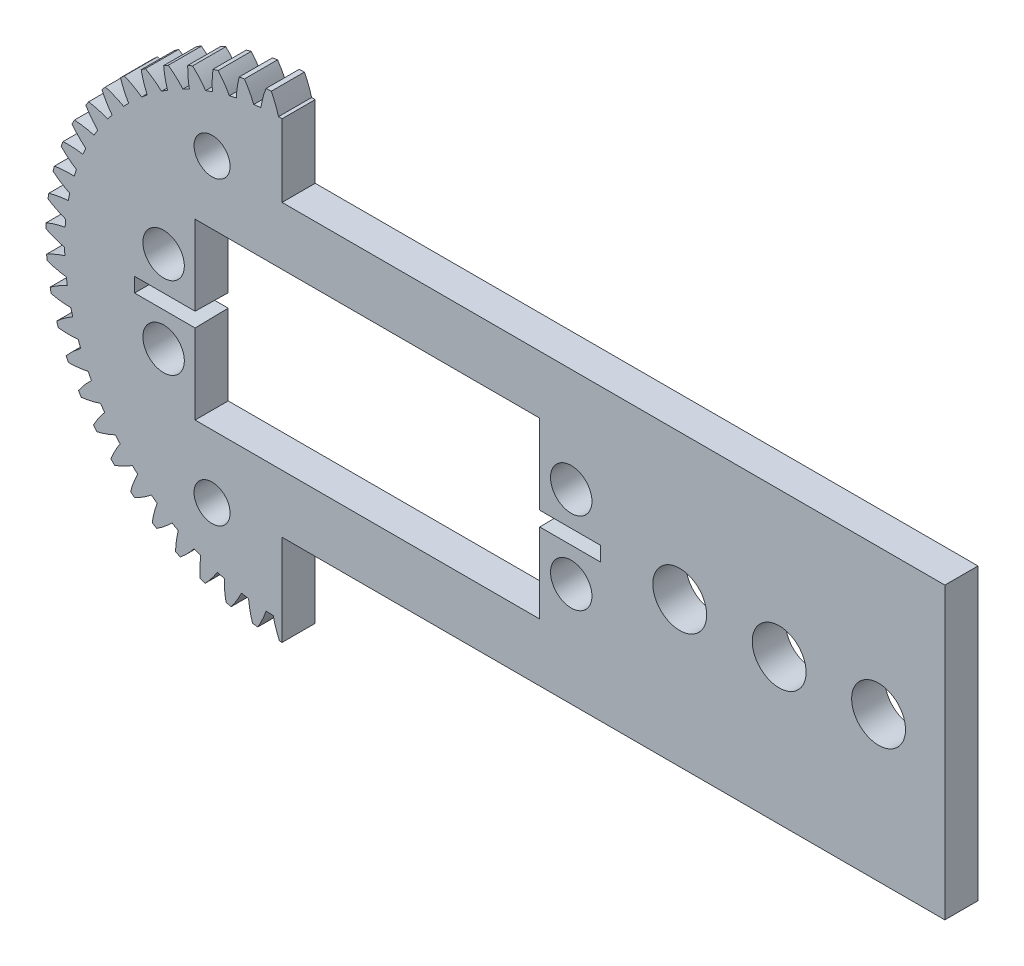
SolidWorks part; units mm, degrees
ref_plane "Front Plane" through (0, 0, 0) normal (0, 0, 1) x (1, 0, 0)
ref_plane "Top Plane" through (0, 0, 0) normal (0, 1, 0) x (1, 0, 0)
ref_plane "Right Plane" through (0, 0, 0) normal (1, 0, 0) x (0, 0, -1)
sketch "Model" plane through (0, 0, 0) normal (0, 0, 1) x (1, 0, 0)
  circle A0 centre (0, 0) radius 2.5
  arc A1 (-28.4774, 1.1339) -> (-28.4957, 0.4937) centre (0, 0) ccw
  arc A2 (-26.1862, 1.814) -> (-28.4774, 1.1339) centre (-24.2203, -9.0089) ccw
  arc A3 (-26.112, 2.6779) -> (-26.1862, 1.814) centre (0, 0) ccw
  arc A4 (-28.2537, 3.7387) -> (-26.112, 2.6779) centre (-22.3294, 13.0071) ccw
  arc A5 (-28.1626, 4.3727) -> (-28.2537, 3.7387) centre (0, 0) ccw
  arc A6 (-25.8088, 4.7871) -> (-28.1626, 4.3727) centre (-25.0894, -6.1893) ccw
  arc A7 (-25.6366, 5.637) -> (-25.8088, 4.7871) centre (0, 0) ccw
  arc A8 (-27.6434, 6.9351) -> (-25.6366, 5.637) centre (-20.7011, 15.4677) ccw
  arc A9 (-27.4805, 7.5545) -> (-27.6434, 6.9351) centre (0, 0) ccw
  arc A10 (-25.0949, 7.6979) -> (-27.4805, 7.5545) centre (-25.6314, -3.289) ccw
  arc A11 (-24.8269, 8.5226) -> (-25.0949, 7.6979) centre (0, 0) ccw
  arc A12 (-26.6726, 10.041) -> (-24.8269, 8.5226) centre (-18.803, 17.7266) ccw
  arc A13 (-26.4403, 10.6378) -> (-26.6726, 10.041) centre (0, 0) ccw
  arc A14 (-24.0538, 10.5083) -> (-26.4403, 10.6378) centre (-25.8392, -0.3458) ccw
  arc A15 (-23.6936, 11.2971) -> (-24.0538, 10.5083) centre (0, 0) ccw
  arc A16 (-25.3542, 13.016) -> (-23.6936, 11.2971) centre (-16.6598, 19.7544) ccw
  arc A17 (-25.0553, 13.5824) -> (-25.3542, 13.016) centre (0, 0) ccw
  arc A18 (-22.6991, 13.1818) -> (-25.0553, 13.5824) centre (-25.7102, 2.6019) ccw
  arc A19 (-22.2513, 13.9244) -> (-22.6991, 13.1818) centre (0, 0) ccw
  arc A20 (-23.7052, 15.8213) -> (-22.2513, 13.9244) centre (-14.2993, 21.5247) ccw
  arc A21 (-23.3437, 16.35) -> (-23.7052, 15.8213) centre (0, 0) ccw
  arc A22 (-21.0486, 15.6834) -> (-23.3437, 16.35) centre (-25.246, 5.5157) ccw
  arc A23 (-20.519, 16.3701) -> (-21.0486, 15.6834) centre (0, 0) ccw
  arc A24 (-21.7472, 18.4203) -> (-20.519, 16.3701) centre (-11.7525, 23.0144) ccw
  arc A25 (-21.3278, 18.9044) -> (-21.7472, 18.4203) centre (0, 0) ccw
  arc A26 (-19.1236, 17.9805) -> (-21.3278, 18.9044) centre (-24.4527, 8.3576) ccw
  arc A27 (-18.5192, 18.6024) -> (-19.1236, 17.9805) centre (0, 0) ccw
  arc A28 (-19.5057, 20.7793) -> (-18.5192, 18.6024) centre (-9.0524, 24.2041) ccw
  arc A29 (-19.0338, 21.2123) -> (-19.5057, 20.7793) centre (0, 0) ccw
  arc A30 (-16.9493, 20.0432) -> (-19.0338, 21.2123) centre (-23.3407, 11.0905) ccw
  arc A31 (-16.278, 20.5921) -> (-16.9493, 20.0432) centre (0, 0) ccw
  arc A32 (-17.0099, 22.8673) -> (-16.278, 20.5921) centre (-6.2344, 25.0782) ccw
  arc A33 (-16.4918, 23.2438) -> (-17.0099, 22.8673) centre (0, 0) ccw
  arc A34 (-14.5541, 21.8446) -> (-16.4918, 23.2438) centre (-21.9243, 13.6788) ccw
  arc A35 (-13.8246, 22.3135) -> (-14.5541, 21.8446) centre (0, 0) ccw
  arc A36 (-14.2923, 24.6572) -> (-13.8246, 22.3135) centre (-3.335, 25.6254) ccw
  arc A37 (-13.7347, 24.9722) -> (-14.2923, 24.6572) centre (0, 0) ccw
  arc A38 (-11.9691, 23.3613) -> (-13.7347, 24.9722) centre (-20.2221, 16.0889) ccw
  arc A39 (-11.1909, 23.7439) -> (-11.9691, 23.3613) centre (0, 0) ccw
  arc A40 (-11.3885, 26.1257) -> (-11.1909, 23.7439) centre (-0.3922, 25.8386) ccw
  arc A41 (-10.7985, 26.375) -> (-11.3885, 26.1257) centre (0, 0) ccw
  arc A42 (-9.2281, 24.5734) -> (-10.7985, 26.375) centre (-18.2563, 18.2891) ccw
  arc A43 (-8.4114, 24.8648) -> (-9.2281, 24.5734) centre (0, 0) ccw
  arc A44 (-8.3361, 27.2536) -> (-8.4114, 24.8648) centre (2.5557, 25.7149) ccw
  arc A45 (-7.7216, 27.434) -> (-8.3361, 27.2536) centre (0, 0) ccw
  arc A46 (-6.3668, 25.4651) -> (-7.7216, 27.434) centre (-16.0525, 20.251) ccw
  arc A47 (-5.5222, 25.6616) -> (-6.3668, 25.4651) centre (0, 0) ccw
  arc A48 (-5.1751, 28.0262) -> (-5.5222, 25.6616) centre (5.4703, 25.2559) ccw
  arc A49 (-4.544, 28.1354) -> (-5.1751, 28.0262) centre (0, 0) ccw
  arc A50 (-3.4225, 26.0249) -> (-4.544, 28.1354) centre (-13.6394, 21.9488) ccw
  arc A51 (-2.561, 26.1238) -> (-3.4225, 26.0249) centre (0, 0) ccw
  arc A52 (-1.9466, 28.4334) -> (-2.561, 26.1238) centre (8.3136, 24.4677) ccw
  arc A53 (-1.3072, 28.47) -> (-1.9466, 28.4334) centre (0, 0) ccw
  arc A54 (-0.4336, 26.2454) -> (-1.3072, 28.47) centre (-11.0486, 23.3605) ccw
  arc A55 (0.4336, 26.2454) -> (-0.4336, 26.2454) centre (0, 0) ccw
  arc A56 (1.3072, 28.47) -> (0.4336, 26.2454) centre (11.0486, 23.3605) ccw
  arc A57 (1.9466, 28.4334) -> (1.3072, 28.47) centre (0, 0) ccw
  arc A58 (2.561, 26.1238) -> (1.9466, 28.4334) centre (-8.3136, 24.4677) ccw
  arc A59 (3.4225, 26.0249) -> (2.561, 26.1238) centre (0, 0) ccw
  arc A60 (4.544, 28.1354) -> (3.4225, 26.0249) centre (13.6394, 21.9488) ccw
  arc A61 (5.1751, 28.0262) -> (4.544, 28.1354) centre (0, 0) ccw
  arc A62 (5.5222, 25.6616) -> (5.1751, 28.0262) centre (-5.4703, 25.2559) ccw
  arc A63 (6.3668, 25.4651) -> (5.5222, 25.6616) centre (0, 0) ccw
  arc A64 (7.7216, 27.434) -> (6.3668, 25.4651) centre (16.0525, 20.251) ccw
  arc A65 (8.3361, 27.2536) -> (7.7216, 27.434) centre (0, 0) ccw
  arc A66 (8.4114, 24.8648) -> (8.3361, 27.2536) centre (-2.5557, 25.7149) ccw
  arc A67 (9.2281, 24.5734) -> (8.4114, 24.8648) centre (0, 0) ccw
  arc A68 (10.7985, 26.375) -> (9.2281, 24.5734) centre (18.2563, 18.2891) ccw
  arc A69 (11.3885, 26.1257) -> (10.7985, 26.375) centre (0, 0) ccw
  arc A70 (11.1909, 23.7439) -> (11.3885, 26.1257) centre (0.3922, 25.8386) ccw
  arc A71 (11.9691, 23.3613) -> (11.1909, 23.7439) centre (0, 0) ccw
  arc A72 (13.7347, 24.9722) -> (11.9691, 23.3613) centre (20.2221, 16.0889) ccw
  arc A73 (14.2923, 24.6572) -> (13.7347, 24.9722) centre (0, 0) ccw
  arc A74 (13.8246, 22.3135) -> (14.2923, 24.6572) centre (3.335, 25.6254) ccw
  arc A75 (14.5541, 21.8446) -> (13.8246, 22.3135) centre (0, 0) ccw
  arc A76 (16.4918, 23.2438) -> (14.5541, 21.8446) centre (21.9243, 13.6788) ccw
  arc A77 (17.0099, 22.8673) -> (16.4918, 23.2438) centre (0, 0) ccw
  arc A78 (16.278, 20.5921) -> (17.0099, 22.8673) centre (6.2344, 25.0782) ccw
  arc A79 (16.9493, 20.0432) -> (16.278, 20.5921) centre (0, 0) ccw
  arc A80 (19.0338, 21.2123) -> (16.9493, 20.0432) centre (23.3407, 11.0905) ccw
  arc A81 (19.5057, 20.7793) -> (19.0338, 21.2123) centre (0, 0) ccw
  arc A82 (18.5192, 18.6024) -> (19.5057, 20.7793) centre (9.0524, 24.2041) ccw
  arc A83 (19.1236, 17.9805) -> (18.5192, 18.6024) centre (0, 0) ccw
  arc A84 (21.3278, 18.9044) -> (19.1236, 17.9805) centre (24.4527, 8.3576) ccw
  arc A85 (21.7472, 18.4203) -> (21.3278, 18.9044) centre (0, 0) ccw
  arc A86 (20.519, 16.3701) -> (21.7472, 18.4203) centre (11.7525, 23.0144) ccw
  arc A87 (21.0486, 15.6834) -> (20.519, 16.3701) centre (0, 0) ccw
  arc A88 (23.3437, 16.35) -> (21.0486, 15.6834) centre (25.246, 5.5157) ccw
  arc A89 (23.7052, 15.8213) -> (23.3437, 16.35) centre (0, 0) ccw
  arc A90 (22.2513, 13.9244) -> (23.7052, 15.8213) centre (14.2993, 21.5247) ccw
  arc A91 (22.6991, 13.1818) -> (22.2513, 13.9244) centre (0, 0) ccw
  arc A92 (25.0553, 13.5824) -> (22.6991, 13.1818) centre (25.7102, 2.6019) ccw
  arc A93 (25.3542, 13.016) -> (25.0553, 13.5824) centre (0, 0) ccw
  arc A94 (23.6936, 11.2971) -> (25.3542, 13.016) centre (16.6598, 19.7544) ccw
  arc A95 (24.0538, 10.5083) -> (23.6936, 11.2971) centre (0, 0) ccw
  arc A96 (26.4403, 10.6378) -> (24.0538, 10.5083) centre (25.8392, -0.3458) ccw
  arc A97 (26.6726, 10.041) -> (26.4403, 10.6378) centre (0, 0) ccw
  arc A98 (24.8269, 8.5226) -> (26.6726, 10.041) centre (18.803, 17.7266) ccw
  arc A99 (25.0949, 7.6979) -> (24.8269, 8.5226) centre (0, 0) ccw
  arc A100 (27.4805, 7.5545) -> (25.0949, 7.6979) centre (25.6314, -3.289) ccw
  arc A101 (27.6434, 6.9351) -> (27.4805, 7.5545) centre (0, 0) ccw
  arc A102 (25.6366, 5.637) -> (27.6434, 6.9351) centre (20.7011, 15.4677) ccw
  arc A103 (25.8088, 4.7871) -> (25.6366, 5.637) centre (0, 0) ccw
  arc A104 (28.1626, 4.3727) -> (25.8088, 4.7871) centre (25.0894, -6.1893) ccw
  arc A105 (28.2537, 3.7387) -> (28.1626, 4.3727) centre (0, 0) ccw
  arc A106 (26.112, 2.6779) -> (28.2537, 3.7387) centre (22.3294, 13.0071) ccw
  arc A107 (26.1862, 1.814) -> (26.112, 2.6779) centre (0, 0) ccw
  arc A108 (28.4774, 1.1339) -> (26.1862, 1.814) centre (24.2203, -9.0089) ccw
  arc A109 (28.4957, 0.4937) -> (28.4774, 1.1339) centre (0, 0) ccw
  arc A110 (26.2471, -0.3161) -> (28.4957, 0.4937) centre (23.6665, 10.377) ccw
  arc A111 (26.2223, -1.1829) -> (26.2471, -0.3161) centre (0, 0) ccw
  arc A112 (28.4211, -2.1197) -> (26.2223, -1.1829) centre (23.0355, -11.7111) ccw
  arc A113 (28.3663, -2.7578) -> (28.4211, -2.1197) centre (0, 0) ccw
  arc A114 (26.04, -3.3059) -> (28.3663, -2.7578) centre (24.6951, 7.6115) ccw
  arc A115 (25.9166, -4.1643) -> (26.04, -3.3059) centre (0, 0) ccw
  arc A116 (27.9942, -5.3456) -> (25.9166, -4.1643) centre (21.5504, -14.2606) ccw
  arc A117 (27.867, -5.9733) -> (27.9942, -5.3456) centre (0, 0) ccw
  arc A118 (25.4934, -6.2527) -> (27.867, -5.9733) centre (25.4018, 4.7469) ccw
  arc A119 (25.2729, -7.0914) -> (25.4934, -6.2527) centre (0, 0) ccw
  arc A120 (27.2024, -8.5019) -> (25.2729, -7.0914) centre (19.7843, -16.6242) ccw
  arc A121 (27.0044, -9.111) -> (27.2024, -8.5019) centre (0, 0) ccw
  arc A122 (24.6145, -9.118) -> (27.0044, -9.111) centre (25.7774, 1.8204) ccw
  arc A123 (24.2999, -9.9261) -> (24.6145, -9.118) centre (0, 0) ccw
  arc A124 (26.0559, -11.5473) -> (24.2999, -9.9261) centre (17.7604, -18.7711) ccw
  arc A125 (25.7898, -12.1299) -> (26.0559, -11.5473) centre (0, 0) ccw
  arc A126 (23.4147, -11.8644) -> (25.7898, -12.1299) centre (25.8168, -1.1299) ccw
  arc A127 (23.01, -12.6314) -> (23.4147, -11.8644) centre (0, 0) ccw
  arc A128 (24.5698, -14.4422) -> (23.01, -12.6314) centre (15.5048, -20.6733) ccw
  arc A129 (24.239, -14.9906) -> (24.5698, -14.4422) centre (0, 0) ccw
  arc A130 (21.9096, -14.4561) -> (24.239, -14.9906) centre (25.5198, -4.0654) ccw
  arc A131 (21.4201, -15.172) -> (21.9096, -14.4561) centre (0, 0) ccw
  arc A132 (22.7633, -17.1488) -> (21.4201, -15.172) centre (13.0472, -22.306) ccw
  arc A133 (22.3722, -17.656) -> (22.7633, -17.1488) centre (0, 0) ccw
  arc A134 (20.1189, -16.8594) -> (22.3722, -17.656) centre (24.89, -6.948) ccw
  arc A135 (19.551, -17.5148) -> (20.1189, -16.8594) centre (0, 0) ccw
  arc A136 (20.6601, -19.6318) -> (19.551, -17.5148) centre (10.4195, -23.6478) ccw
  arc A137 (20.2138, -20.0911) -> (20.6601, -19.6318) centre (0, 0) ccw
  arc A138 (18.0659, -19.0429) -> (20.2138, -20.0911) centre (23.9357, -9.7399) ccw
  arc A139 (17.4271, -19.6293) -> (18.0659, -19.0429) centre (0, 0) ccw
  arc A140 (18.2876, -21.8589) -> (17.4271, -19.6293) centre (7.6559, -24.6814) ccw
  arc A141 (17.7918, -22.2644) -> (18.2876, -21.8589) centre (0, 0) ccw
  arc A142 (15.7774, -20.9781) -> (17.7918, -22.2644) centre (22.6694, -12.4049) ccw
  arc A143 (15.0759, -21.4878) -> (15.7774, -20.9781) centre (0, 0) ccw
  arc A144 (15.6767, -23.8011) -> (15.0759, -21.4878) centre (4.7925, -25.3933) ccw
  arc A145 (15.1379, -24.1473) -> (15.6767, -23.8011) centre (0, 0) ccw
  arc A146 (13.2833, -22.6399) -> (15.1379, -24.1473) centre (21.1076, -14.9082) ccw
  arc A147 (12.5282, -23.0663) -> (13.2833, -22.6399) centre (0, 0) ccw
  arc A148 (12.8614, -25.433) -> (12.5282, -23.0663) centre (1.8667, -25.774) ccw
  arc A149 (12.2866, -25.7155) -> (12.8614, -25.433) centre (0, 0) ccw
  arc A150 (10.6159, -24.0065) -> (12.2866, -25.7155) centre (19.2706, -17.2171) ccw
  arc A151 (9.8172, -24.3441) -> (10.6159, -24.0065) centre (0, 0) ccw
  arc A152 (9.8784, -26.7333) -> (9.8172, -24.3441) centre (-1.0835, -25.8188) ccw
  arc A153 (9.2752, -26.9485) -> (9.8784, -26.7333) centre (0, 0) ccw
  arc A154 (7.8102, -25.0601) -> (9.2752, -26.9485) centre (17.1824, -19.3015) ccw
  arc A155 (6.9782, -25.3044) -> (7.8102, -25.0601) centre (0, 0) ccw
  arc A156 (6.7667, -27.6851) -> (6.9782, -25.3044) centre (-4.0196, -25.527) ccw
  arc A157 (6.1428, -27.8301) -> (6.7667, -27.6851) centre (0, 0) ccw
  arc A158 (4.9027, -25.7871) -> (6.1428, -27.8301) centre (14.8702, -21.1344) ccw
  arc A159 (4.0482, -25.935) -> (4.9027, -25.7871) centre (0, 0) ccw
  arc A160 (3.5667, -28.2759) -> (4.0482, -25.935) centre (-6.9032, -24.9024) ccw
  arc A161 (2.9304, -28.3489) -> (3.5667, -28.2759) centre (0, 0) ccw
  arc A162 (1.9312, -26.1779) -> (2.9304, -28.3489) centre (12.3642, -22.6917) ccw
  arc A163 (1.0654, -26.2274) -> (1.9312, -26.1779) centre (0, 0) ccw
  arc A164 (0.3202, -28.4982) -> (1.0654, -26.2274) centre (-9.6969, -23.9532) ccw
  arc A165 (-0.3202, -28.4982) -> (0.3202, -28.4982) centre (0, 0) ccw
  arc A166 (-1.0654, -26.2274) -> (-0.3202, -28.4982) centre (9.6969, -23.9532) ccw
  arc A167 (-1.9312, -26.1779) -> (-1.0654, -26.2274) centre (0, 0) ccw
  arc A168 (-2.9304, -28.3489) -> (-1.9312, -26.1779) centre (-12.3642, -22.6917) ccw
  arc A169 (-3.5667, -28.2759) -> (-2.9304, -28.3489) centre (0, 0) ccw
  arc A170 (-4.0482, -25.935) -> (-3.5667, -28.2759) centre (6.9032, -24.9024) ccw
  arc A171 (-4.9027, -25.7871) -> (-4.0482, -25.935) centre (0, 0) ccw
  arc A172 (-6.1428, -27.8301) -> (-4.9027, -25.7871) centre (-14.8702, -21.1344) ccw
  arc A173 (-6.7667, -27.6851) -> (-6.1428, -27.8301) centre (0, 0) ccw
  arc A174 (-6.9782, -25.3044) -> (-6.7667, -27.6851) centre (4.0196, -25.527) ccw
  arc A175 (-7.8102, -25.0601) -> (-6.9782, -25.3044) centre (0, 0) ccw
  arc A176 (-9.2752, -26.9485) -> (-7.8102, -25.0601) centre (-17.1824, -19.3015) ccw
  arc A177 (-9.8784, -26.7333) -> (-9.2752, -26.9485) centre (0, 0) ccw
  arc A178 (-9.8172, -24.3441) -> (-9.8784, -26.7333) centre (1.0835, -25.8188) ccw
  arc A179 (-10.6159, -24.0065) -> (-9.8172, -24.3441) centre (0, 0) ccw
  arc A180 (-12.2866, -25.7155) -> (-10.6159, -24.0065) centre (-19.2706, -17.2171) ccw
  arc A181 (-12.8614, -25.433) -> (-12.2866, -25.7155) centre (0, 0) ccw
  arc A182 (-12.5282, -23.0663) -> (-12.8614, -25.433) centre (-1.8667, -25.774) ccw
  arc A183 (-13.2833, -22.6399) -> (-12.5282, -23.0663) centre (0, 0) ccw
  arc A184 (-15.1379, -24.1473) -> (-13.2833, -22.6399) centre (-21.1076, -14.9082) ccw
  arc A185 (-15.6767, -23.8011) -> (-15.1379, -24.1473) centre (0, 0) ccw
  arc A186 (-15.0759, -21.4878) -> (-15.6767, -23.8011) centre (-4.7925, -25.3933) ccw
  arc A187 (-15.7774, -20.9781) -> (-15.0759, -21.4878) centre (0, 0) ccw
  arc A188 (-17.7918, -22.2644) -> (-15.7774, -20.9781) centre (-22.6694, -12.4049) ccw
  arc A189 (-18.2876, -21.8589) -> (-17.7918, -22.2644) centre (0, 0) ccw
  arc A190 (-17.4271, -19.6293) -> (-18.2876, -21.8589) centre (-7.6559, -24.6814) ccw
  arc A191 (-18.0659, -19.0429) -> (-17.4271, -19.6293) centre (0, 0) ccw
  arc A192 (-20.2138, -20.0911) -> (-18.0659, -19.0429) centre (-23.9357, -9.7399) ccw
  arc A193 (-20.6601, -19.6318) -> (-20.2138, -20.0911) centre (0, 0) ccw
  arc A194 (-19.551, -17.5148) -> (-20.6601, -19.6318) centre (-10.4195, -23.6478) ccw
  arc A195 (-20.1189, -16.8594) -> (-19.551, -17.5148) centre (0, 0) ccw
  arc A196 (-22.3722, -17.656) -> (-20.1189, -16.8594) centre (-24.89, -6.948) ccw
  arc A197 (-22.7633, -17.1488) -> (-22.3722, -17.656) centre (0, 0) ccw
  arc A198 (-21.4201, -15.172) -> (-22.7633, -17.1488) centre (-13.0472, -22.306) ccw
  arc A199 (-21.9096, -14.4561) -> (-21.4201, -15.172) centre (0, 0) ccw
  arc A200 (-24.239, -14.9906) -> (-21.9096, -14.4561) centre (-25.5198, -4.0654) ccw
  arc A201 (-24.5698, -14.4422) -> (-24.239, -14.9906) centre (0, 0) ccw
  arc A202 (-23.01, -12.6314) -> (-24.5698, -14.4422) centre (-15.5048, -20.6733) ccw
  arc A203 (-23.4147, -11.8644) -> (-23.01, -12.6314) centre (0, 0) ccw
  arc A204 (-25.7898, -12.1299) -> (-23.4147, -11.8644) centre (-25.8168, -1.1299) ccw
  arc A205 (-26.0559, -11.5473) -> (-25.7898, -12.1299) centre (0, 0) ccw
  arc A206 (-24.2999, -9.9261) -> (-26.0559, -11.5473) centre (-17.7604, -18.7711) ccw
  arc A207 (-24.6145, -9.118) -> (-24.2999, -9.9261) centre (0, 0) ccw
  arc A208 (-27.0044, -9.111) -> (-24.6145, -9.118) centre (-25.7774, 1.8204) ccw
  arc A209 (-27.2024, -8.5019) -> (-27.0044, -9.111) centre (0, 0) ccw
  arc A210 (-25.2729, -7.0914) -> (-27.2024, -8.5019) centre (-19.7843, -16.6242) ccw
  arc A211 (-25.4934, -6.2527) -> (-25.2729, -7.0914) centre (0, 0) ccw
  arc A212 (-27.867, -5.9733) -> (-25.4934, -6.2527) centre (-25.4018, 4.7469) ccw
  arc A213 (-27.9942, -5.3456) -> (-27.867, -5.9733) centre (0, 0) ccw
  arc A214 (-25.9166, -4.1643) -> (-27.9942, -5.3456) centre (-21.5504, -14.2606) ccw
  arc A215 (-26.04, -3.3059) -> (-25.9166, -4.1643) centre (0, 0) ccw
  arc A216 (-28.3663, -2.7578) -> (-26.04, -3.3059) centre (-24.6951, 7.6115) ccw
  arc A217 (-28.4211, -2.1197) -> (-28.3663, -2.7578) centre (0, 0) ccw
  arc A218 (-26.2223, -1.1829) -> (-28.4211, -2.1197) centre (-23.0355, -11.7111) ccw
  arc A219 (-26.2471, -0.3161) -> (-26.2223, -1.1829) centre (0, 0) ccw
  arc A220 (-28.4957, 0.4937) -> (-26.2471, -0.3161) centre (-23.6665, 10.377) ccw
extrude "Boss-Extrude1" add sketch "Model" along normal blind 4
sketch "Sketch3" plane through (0, 0, 4) normal (0, 0, 1) x (1, 0, 0)
  circle A0 centre (0, 0) radius 27.5 construction
  dimension "D1" = 55
sketch "Sketch2" plane through (0, 0, 0) normal (0, 0, 1) x (1, 0, 0)
  line L1 (-43.8296, -31.5342) -> (43.8296, -31.5342)
  line L2 (-43.8296, -31.5342) -> (-43.8296, 31.5342)
  line L3 (-43.8296, 31.5342) -> (43.8296, 31.5342)
  line L4 (43.8296, -31.5342) -> (43.8296, 31.5342)
  line L5 (0, 31.5342) -> (0, -31.5342)
  line L6 (-43.8296, 0) -> (43.8296, 0) construction
  point P0 (0, 0)
extrude "Cut-Extrude2" cut sketch "Sketch2" along normal blind 4 contours L5 L6 L4 L3 | L6 L5 L1 L4
sketch "Sketch4" plane through (0, 0, 0) normal (0, 0, 1) x (1, 0, 0)
  line L0 (0, 0) -> (40, 0) construction
  line L1 (0, 26.249) -> (0, 2.5) construction
  line L2 (80, -17.5) -> (0, -17.5)
  line L3 (80, -17.5) -> (80, 17.5)
  line L4 (80, 17.5) -> (0, 17.5)
  line L5 (0, -17.5) -> (0, 17.5)
  line L6 (40, 17.5) -> (40, -17.5) construction
  line L7 (80, 0) -> (0, 0) construction
  dimension "D1" = 35
  dimension "D2" = 80
extrude "Boss-Extrude3" add sketch "Sketch4" along normal blind 4
sketch "Sketch5" plane through (0, 0, 4) normal (0, 0, 1) x (1, 0, 0)
  line L0 (80, 0) -> (-33.2259, 0) construction
  line L1 (80, -17.5) -> (80, 17.5) construction
  line L2 (0, 17.5) -> (0, -17.5) construction
  line L4 (-10, -10) -> (30.6, -10) construction
  line L5 (-10, -10) -> (-10, 10) construction
  line L6 (-10, 10) -> (30.6, 10) construction
  line L7 (30.6, -10) -> (30.6, 10) construction
  line L8 (-10.5, -10.5) -> (31.1, -10.5)
  line L9 (-10, 0) -> (30.6, 0) construction
  line L10 (-10.5, -10.5) -> (-10.5, 10.5)
  line L11 (-10.5, 10.5) -> (31.1, 10.5)
  line L12 (31.1, -10.5) -> (31.1, 10.5)
  line L13 (10.3, 10.5) -> (10.3, -10.5) construction
  line L14 (-10.5, 0) -> (31.1, 0) construction
  point P9 (16.3751, 0)
  point P13 (10.3, 0)
  point P17 (0, 0)
  point P18 (0, 0)
  point P19 (-7.4354, 10.5)
  dimension "D1" = 40.6
  dimension "D2" = 20
  dimension "D3" = 0.5
  dimension "D4" = 0.5
  dimension "D5" = 0.5
  dimension "D6" = 10
extrude "Cut-Extrude3" cut sketch "Sketch5" against normal blind 4
sketch "Sketch6" plane through (0, 0, 4) normal (0, 0, 1) x (1, 0, 0)
  line L0 (10.3, 10.5) -> (10.3, -10.5) construction
  line L1 (31.1, 10.5) -> (-10.5, 10.5) construction
  line L2 (-10.5, -10.5) -> (31.1, -10.5) construction
  line L3 (80, 0) -> (10.3, 0) construction
  line L4 (80, -17.5) -> (80, 17.5) construction
  line L5 (34.9, 4.95) -> (34.9, -4.95) construction
  circle A0 centre (34.9, 4.95) radius 2.5
  circle A1 centre (34.9, -4.95) radius 2.5
  circle A4 centre (-14.3, -4.95) radius 2.5
  circle A5 centre (-14.3, 4.95) radius 2.5
  point P13 (34.9, 0)
  dimension "D1" = 5
  dimension "D2" = 9.9
  dimension "D3" = 24.6
extrude "Cut-Extrude4" cut sketch "Sketch6" against normal blind 4
sketch "Sketch7" plane through (0, 0, 4) normal (0, 0, 1) x (1, 0, 0)
  line L0 (0, 0) -> (-25.2928, 0) construction
  line L1 (0, 0) -> (-15.5396, 15.5396) construction
  line L2 (0, 0) -> (-8.4524, 18.1262) construction
  circle A0 centre (-8.4524, 18.1262) radius 2.175
  circle A1 centre (-8.4524, -18.1262) radius 2.175
  point P10 (0, 0)
  dimension "D1" = 4.35
  dimension "D2" = 45
  dimension "D3" = 20
  dimension "D4" = 20
  dimension "D5" = 2
extrude "Cut-Extrude5" cut sketch "Sketch7" against normal blind 4
sketch "Sketch8" plane through (0, 0, 4) normal (0, 0, 1) x (1, 0, 0)
  line L0 (80, 0) -> (0, 0) construction
  line L1 (80, -17.5) -> (80, 17.5) construction
  circle A0 centre (72, 0) radius 3.25
  dimension "D1" = 6.5
  dimension "D2" = 8
extrude "Cut-Extrude6" cut sketch "Sketch8" against normal blind 400
pattern_linear "LPattern1" count 3 spacing 12 along (-1, 0, 0) of "Cut-Extrude6"
sketch "Sketch9" plane through (0, 0, 4) normal (0, 0, 1) x (1, 0, 0)
  line L0 (29.4058, 0) -> (38.4058, 0)
  line L4 (31.1, -10.5) -> (31.1, 10.5) construction
  line L5 (10.3, 10.5) -> (10.3, -10.5) construction
  line L6 (31.1, 10.5) -> (-10.5, 10.5) construction
  line L7 (-10.5, -10.5) -> (31.1, -10.5) construction
  line L8 (-8.8058, 0) -> (-17.8058, 0)
  point P3 (31.1, 0)
  dimension "D1" = 9
extrude "Cut-Extrude-Thin1" cut sketch "Sketch9" against normal through all draft 1 thin thin type mid plane wall 1.75
